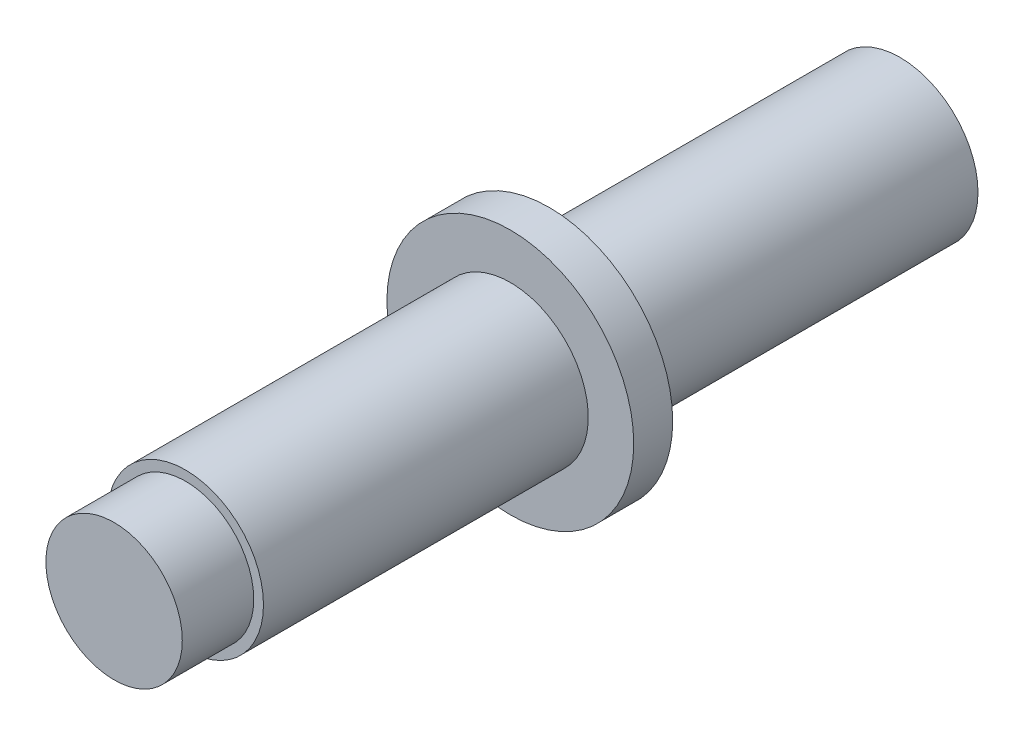
SolidWorks part; units mm, degrees
ref_plane "Front" through (0, 0, 0) normal (0, 0, 1) x (1, 0, 0)
ref_plane "Top" through (0, 0, 0) normal (0, 1, 0) x (1, 0, 0)
ref_plane "Right" through (0, 0, 0) normal (1, 0, 0) x (0, 0, -1)
other "Configuration Table"
sketch "Эскиз1" plane through (0, 0, 0) normal (0, 0, 1) x (1, 0, 0)
  circle A0 centre (0, 0) radius 6
extrude "Бобышка-Вытянуть1" add sketch "Эскиз1" along normal blind 55
sketch "Эскиз2" plane through (0, 0, 55) normal (0, 0, 1) x (1, 0, 0)
  circle A0 centre (0, 0) radius 5.25
extrude "Бобышка-Вытянуть2" add sketch "Эскиз2" along normal blind 5.5
sketch "Эскиз3" plane through (0, 0, 0) normal (0, 0, -1) x (-1, 0, 0)
  circle A0 centre (0, 0) radius 9.5
extrude "Бобышка-Вытянуть3" add sketch "Эскиз3" along normal blind 3 from offset 30 offset against normal yes
